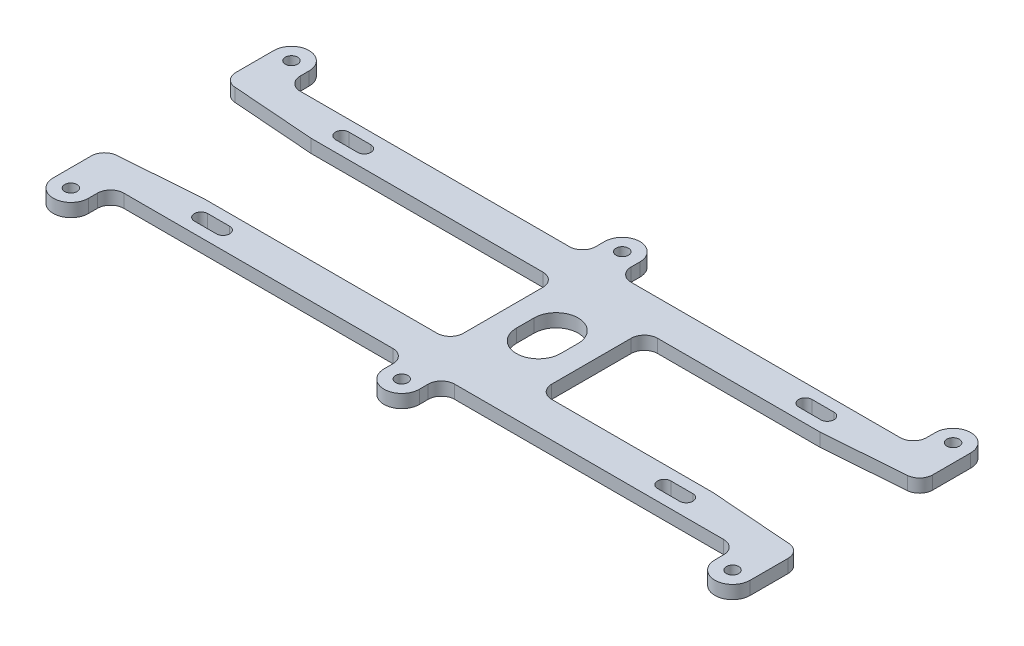
SolidWorks part; units mm, degrees
ref_plane "Front Plane" through (0, 0, 0) normal (0, 0, 1) x (1, 0, 0)
ref_plane "Top Plane" through (0, 0, 0) normal (0, 1, 0) x (1, 0, 0)
ref_plane "Right Plane" through (0, 0, 0) normal (1, 0, 0) x (0, 0, -1)
sketch "Sketch1" plane through (0, 0, 0) normal (0, 1, 0) x (1, 0, 0)
  line L0 (55.4997, -17.5) -> (50.4997, -17.5)
  line L1 (50.4997, -14.5) -> (55.4997, -14.5)
  line L2 (50.4997, 17.5) -> (55.4997, 17.5)
  line L3 (55.4997, 14.5) -> (50.4997, 14.5)
  line L4 (12.9997, 2) -> (12.9997, -2)
  line L5 (2.9997, -2) -> (2.9997, 2)
  line L6 (-49.5003, -17.5) -> (-54.5003, -17.5)
  line L7 (-54.5003, -14.5) -> (-49.5003, -14.5)
  line L8 (-54.5003, 17.5) -> (-49.5003, 17.5)
  line L9 (-49.5003, 14.5) -> (-54.5003, 14.5)
  line L10 (-76.2241, 13.4002) -> (-57.5546, 12)
  line L11 (-57.5546, 12) -> (-5.0003, 12)
  line L12 (-2.0003, 9) -> (-2.0003, -9.0084)
  line L13 (-5.0003, -12.0084) -> (-57.779, -12.0084)
  line L14 (-57.779, -12.0084) -> (-76.2247, -13.3918)
  line L15 (-79.0003, -16.3834) -> (-79.0003, -25)
  line L16 (-71.0003, -25) -> (-71.0003, -23)
  line L17 (-68.0003, -20) -> (-7.0003, -20)
  line L18 (-4.0003, -23) -> (-4.0003, -25)
  line L19 (3.9997, -25) -> (3.9997, -23)
  line L20 (6.9997, -20) -> (67.9991, -20)
  line L21 (70.9991, -23) -> (70.9991, -25)
  line L22 (78.9991, -25) -> (78.9991, -16.3918)
  line L23 (76.2234, -13.4002) -> (57.554, -12)
  line L24 (57.554, -12) -> (20.9997, -12)
  line L25 (17.9997, -9) -> (17.9997, 9.0084)
  line L26 (20.9997, 12.0084) -> (57.7784, 12.0084)
  line L27 (57.7784, 12.0084) -> (76.2241, 13.3918)
  line L28 (79.0003, 16.3834) -> (79.0003, 25)
  line L29 (71.0003, 25) -> (71.0003, 23)
  line L30 (68.0003, 20) -> (7.0003, 20)
  line L31 (4.0003, 23) -> (4.0003, 25)
  line L32 (-3.9997, 25) -> (-3.9997, 23)
  line L33 (-6.9997, 20) -> (-67.9997, 20)
  line L34 (-70.9997, 23) -> (-70.9997, 25)
  line L35 (-78.9997, 25) -> (-78.9997, 16.3918)
  circle A0 centre (74.9997, 25) radius 1.4
  circle A1 centre (74.9997, -25) radius 1.4
  arc A2 (55.4997, -17.5) -> (55.4997, -14.5) centre (55.4997, -16) ccw
  arc A3 (50.4997, -14.5) -> (50.4997, -17.5) centre (50.4997, -16) ccw
  arc A4 (55.4997, 14.5) -> (55.4997, 17.5) centre (55.4997, 16) ccw
  arc A5 (50.4997, 17.5) -> (50.4997, 14.5) centre (50.4997, 16) ccw
  arc A6 (-78.9997, 16.3918) -> (-76.2241, 13.4002) centre (-75.9997, 16.3918) ccw
  arc A7 (-2.0003, 9) -> (-5.0003, 12) centre (-5.0003, 9) ccw
  arc A8 (-5.0003, -12.0084) -> (-2.0003, -9.0084) centre (-5.0003, -9.0084) ccw
  arc A9 (-76.2247, -13.3918) -> (-79.0003, -16.3834) centre (-76.0003, -16.3834) ccw
  arc A10 (-79.0003, -25) -> (-71.0003, -25) centre (-75.0003, -25) ccw
  arc A11 (-68.0003, -20) -> (-71.0003, -23) centre (-68.0003, -23) ccw
  arc A12 (-4.0003, -23) -> (-7.0003, -20) centre (-7.0003, -23) ccw
  arc A13 (-4.0003, -25) -> (3.9997, -25) centre (-0.0003, -25) ccw
  arc A14 (6.9997, -20) -> (3.9997, -23) centre (6.9997, -23) ccw
  arc A15 (70.9991, -23) -> (67.9991, -20) centre (67.9991, -23) ccw
  arc A16 (70.9991, -25) -> (78.9991, -25) centre (74.9991, -25) ccw
  arc A17 (78.9991, -16.3918) -> (76.2234, -13.4002) centre (75.9991, -16.3918) ccw
  arc A18 (17.9997, -9) -> (20.9997, -12) centre (20.9997, -9) ccw
  arc A19 (20.9997, 12.0084) -> (17.9997, 9.0084) centre (20.9997, 9.0084) ccw
  arc A20 (76.2241, 13.3918) -> (79.0003, 16.3834) centre (76.0003, 16.3835) ccw
  arc A21 (79.0003, 25) -> (71.0003, 25) centre (75.0003, 25) ccw
  arc A22 (68.0003, 20) -> (71.0003, 23) centre (68.0003, 23) ccw
  arc A23 (4.0003, 23) -> (7.0003, 20) centre (7.0003, 23) ccw
  arc A24 (4.0003, 25) -> (-3.9997, 25) centre (0.0003, 25) ccw
  arc A25 (-6.9997, 20) -> (-3.9997, 23) centre (-6.9997, 23) ccw
  arc A26 (-70.9997, 23) -> (-67.9997, 20) centre (-67.9997, 23) ccw
  arc A27 (-70.9997, 25) -> (-78.9997, 25) centre (-74.9997, 25) ccw
  circle A28 centre (-0.0003, -25) radius 1.4
  circle A29 centre (-0.0003, 25) radius 1.4
  arc A30 (12.9997, 2) -> (2.9997, 2) centre (7.9997, 2) ccw
  arc A31 (2.9997, -2) -> (12.9997, -2) centre (7.9997, -2) ccw
  arc A32 (-49.5003, -17.5) -> (-49.5003, -14.5) centre (-49.5003, -16) ccw
  arc A33 (-54.5003, -14.5) -> (-54.5003, -17.5) centre (-54.5003, -16) ccw
  arc A34 (-49.5003, 14.5) -> (-49.5003, 17.5) centre (-49.5003, 16) ccw
  arc A35 (-54.5003, 17.5) -> (-54.5003, 14.5) centre (-54.5003, 16) ccw
  circle A36 centre (-75.0003, 25) radius 1.4
  circle A37 centre (-75.0003, -25) radius 1.4
  dimension "D1" = 2.8
  dimension "D2" = 18.0084
extrude "Boss-Extrude1" add sketch "Sketch1" along normal blind 3
